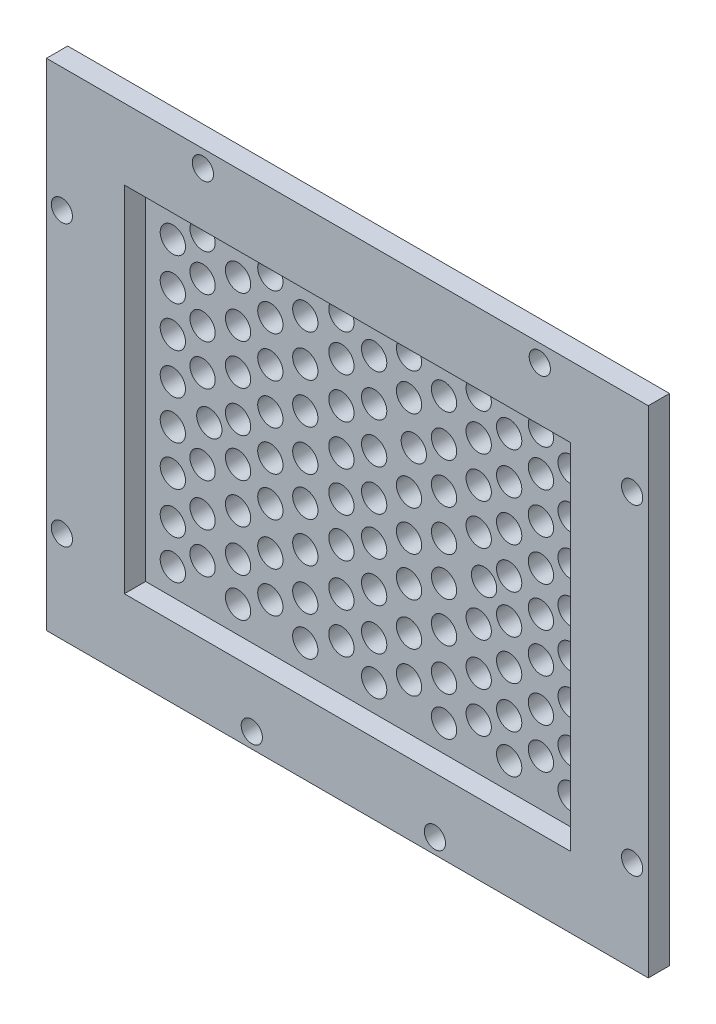
SolidWorks part; units mm, degrees
ref_plane "Front Plane" through (0, 0, 0) normal (0, 0, 1) x (1, 0, 0)
ref_plane "Top Plane" through (0, 0, 0) normal (0, 1, 0) x (1, 0, 0)
ref_plane "Right Plane" through (0, 0, 0) normal (1, 0, 0) x (0, 0, -1)
sketch "Sketch1" plane through (0, 0, 0) normal (0, 0, 1) x (1, 0, 0)
  line L1 (-42.5, 35) -> (42.5, 35)
  line L2 (-42.5, 35) -> (-42.5, -35)
  line L3 (-42.5, -35) -> (42.5, -35)
  line L4 (42.5, 35) -> (42.5, -35)
  line L5 (-42.5, 35) -> (42.5, -35) construction
  line L6 (-42.5, -35) -> (42.5, 35) construction
  point P0 (0, 0)
  dimension "D1" = 85
  dimension "D2" = 70
extrude "Boss-Extrude1" add sketch "Sketch1" along normal blind 6
sketch "Sketch2" plane through (0, 0, 0) normal (0, 0, -1) x (-1, 0, 0)
  line L1 (38, -30.5) -> (-38, -30.5)
  line L2 (38, -30.5) -> (38, 30.5)
  line L3 (38, 30.5) -> (-38, 30.5)
  line L4 (-38, -30.5) -> (-38, 30.5)
  line L5 (38, -30.5) -> (-38, 30.5) construction
  line L6 (38, 30.5) -> (-38, -30.5) construction
  line L7 (32.5, -26.0855) -> (-32.5, -26.0855)
  line L8 (32.5, -26.0855) -> (32.5, 26.0855)
  line L9 (32.5, 26.0855) -> (-32.5, 26.0855)
  line L10 (-32.5, -26.0855) -> (-32.5, 26.0855)
  line L11 (32.5, -26.0855) -> (-32.5, 26.0855) construction
  line L12 (32.5, 26.0855) -> (-32.5, -26.0855) construction
  point P0 (0, 0)
  point P6 (0, 0)
  dimension "D1" = 76
  dimension "D2" = 61
  dimension "D3" = 65
extrude "Cut-Extrude1" cut sketch "Sketch2" against normal blind 5
sketch "Sketch8" plane through (0, 0, 6) normal (0, 0, 1) x (1, 0, 0)
  line L1 (-31.5, 25) -> (31.5, 25)
  line L2 (-31.5, 25) -> (-31.5, -25)
  line L3 (-31.5, -25) -> (31.5, -25)
  line L4 (31.5, 25) -> (31.5, -25)
  line L5 (-31.5, 25) -> (31.5, -25) construction
  line L6 (-31.5, -25) -> (31.5, 25) construction
  point P0 (0, 0)
  dimension "D1" = 63
  dimension "D2" = 50
extrude "Cut-Extrude2" cut sketch "Sketch8" against normal blind 3
sketch "Sketch19" plane through (0, 0, 0) normal (0, 0, -1) x (-1, 0, 0)
  line L1 (42.5, 35) -> (-42.5, 35)
  line L2 (42.5, 35) -> (42.5, -35)
  line L3 (42.5, -35) -> (-42.5, -35)
  line L4 (-42.5, 35) -> (-42.5, -35)
  line L5 (38, 30.5) -> (-38, 30.5)
  line L6 (38, 30.5) -> (38, -30.5)
  line L7 (38, -30.5) -> (-38, -30.5)
  line L8 (-38, 30.5) -> (-38, -30.5)
extrude "Cut-Extrude3" cut sketch "Sketch19" against normal blind 3
hole_wizard "9/64 (0.14063) Diameter Hole3" positions "Sketch16" profile "Sketch17" hole size "9/64" standard "ANSI Inch" end condition through all
sketch "Sketch16" plane through (0, 0, 3) normal (0, 0, 1) x (1, 0, 0)
  point P0 (28.5299, -21.2502)
  point P2 (28.5299, -15.7459)
  point P4 (28.5299, -9.8359)
  point P6 (28.5299, -4.1565)
  point P8 (28.5299, 1.3478)
  point P10 (28.5299, 7.1342)
  point P12 (28.5299, 12.8672)
  point P14 (28.5299, 18.7586)
  point P16 (24.3337, 16.0835)
  point P18 (24.3337, 21.3242)
  point P20 (24.3337, 10.3073)
  point P22 (24.3337, 4.5476)
  point P24 (24.3337, -1.0885)
  point P26 (24.3337, -6.6814)
  point P28 (24.3337, -12.7046)
  point P30 (24.3337, -18.4375)
  point P32 (19.8485, -21.2502)
  point P34 (19.8485, -15.7459)
  point P36 (19.8485, -9.8359)
  point P38 (19.8485, -4.1565)
  point P40 (19.8485, 1.3478)
  point P42 (19.8485, 7.1342)
  point P44 (19.8485, 12.8672)
  point P46 (19.8485, 18.7586)
  point P48 (15.5475, 21.3242)
  point P50 (15.5475, 16.0835)
  point P52 (15.5475, 10.3073)
  point P54 (15.5475, 4.5476)
  point P56 (16.308, -1.0885)
  point P58 (15.5475, -6.6814)
  point P60 (15.5475, -12.7046)
  point P62 (15.5475, -18.4375)
  point P64 (10.6485, -21.2502)
  point P66 (10.6485, -15.7459)
  point P68 (10.6485, -9.8359)
  point P70 (10.6485, -4.1565)
  point P72 (10.6485, 1.3478)
  point P74 (10.6485, 7.1342)
  point P76 (10.6485, 12.8672)
  point P78 (10.6485, 18.7586)
  point P80 (5.7056, 21.3242)
  point P82 (5.7056, 16.0835)
  point P84 (6.3821, 10.3073)
  point P86 (5.7056, 4.5476)
  point P88 (5.7056, -1.0885)
  point P90 (5.7056, -6.6814)
  point P92 (5.7056, -12.7046)
  point P94 (5.7056, -18.4375)
  point P96 (0.7819, -21.2502)
  point P98 (0.7819, -15.7459)
  point P100 (0.7819, -9.8359)
  point P102 (0.7819, -4.1565)
  point P104 (0.7819, 1.3478)
  point P106 (0.7819, 7.1342)
  point P108 (0.7819, 12.8672)
  point P110 (0.7819, 18.7586)
  point P112 (-3.8442, 21.3242)
  point P114 (-3.8442, 16.0835)
  point P116 (-3.8442, 10.3073)
  point P118 (-3.8442, 4.5476)
  point P120 (-3.8442, -1.0885)
  point P122 (-3.8442, -6.6814)
  point P124 (-3.8442, -12.7046)
  point P126 (-3.8442, -18.4375)
  point P128 (-8.9449, -21.2502)
  point P130 (-8.9449, -15.7459)
  point P132 (-8.9449, -9.8359)
  point P134 (-8.9449, -4.1565)
  point P136 (-8.9449, 1.3478)
  point P138 (-8.9449, 7.1342)
  point P140 (-8.9449, 12.8672)
  point P142 (-8.9449, 18.7586)
  point P144 (-13.8796, 21.3242)
  point P146 (-13.8796, 16.0835)
  point P148 (-13.8796, 10.3073)
  point P150 (-13.8796, 4.5476)
  point P152 (-13.8796, -1.0885)
  point P154 (-13.8796, -6.6814)
  point P156 (-13.8796, -12.7046)
  point P158 (-13.8796, -18.4375)
  point P160 (-18.4432, -21.2502)
  point P162 (-18.4432, -15.7459)
  point P164 (-18.4432, -9.8359)
  point P166 (-18.4432, -4.1565)
  point P168 (-18.4432, 1.3478)
  point P170 (-18.4432, 7.1342)
  point P172 (-18.4432, 12.8672)
  point P174 (-18.4432, 18.7586)
  point P176 (-23.4561, 21.3242)
  point P178 (-23.4561, 16.0835)
  point P180 (-23.4561, 10.3073)
  point P182 (-23.4561, 4.5476)
  point P184 (-22.5022, -1.0885)
  point P186 (-23.4561, -6.6814)
  point P188 (-23.4561, -12.7046)
  point P190 (-23.4561, -18.4375)
  point P192 (-27.6514, -21.2502)
  point P194 (-27.6514, -15.7459)
  point P196 (-27.6514, -9.8359)
  point P198 (-27.6514, -4.1565)
  point P200 (-27.6514, 1.3478)
  point P202 (-27.6514, 7.1342)
  point P204 (-27.6514, 12.8672)
  point P206 (-27.6514, 18.7586)
sketch "Sketch17" plane through (28.5299, -21.2502, 3) normal (1, 0, 0) x (0, -1, 0)
  line L0 (0, 0) -> (0, 3)
  line L1 (0, 3) -> (1.786, 3)
  line L2 (1.786, 3) -> (1.786, 0)
  line L5 (1.786, 0) -> (0, 0)
  line L11 (0, -6.35) -> (0, 107.95) construction
  dimension "Thru Hole Dia." = 3.572
  dimension "Thru Hole Depth" = 3
hole_wizard "Ø3.0mm Dowel Hole1" positions "Sketch24" profile "Sketch25" hole size "Ø3.0" standard "ANSI Metric" end condition up to next
sketch "Sketch24" plane through (0, 0, 3) normal (0, 0, -1) x (-1, 0, 0)
  point P0 (13.4989, -32.8457)
  point P2 (-12.3633, -32.8457)
  point P4 (40.3256, -22.041)
  point P6 (40.3256, 17.4959)
  point P8 (20.4097, 32.5889)
  point P10 (-27.1767, 32.5889)
  point P12 (-40.218, 23.3314)
  point P14 (-40.218, -22.041)
sketch "Sketch25" plane through (-13.4989, -32.8457, 3) normal (1, 0, 0) x (0, 1, 0)
  line L0 (0, 0) -> (0, 3)
  line L1 (0, 3) -> (1.5, 3)
  line L2 (1.5, 3) -> (1.5, 0)
  line L5 (1.5, 0) -> (0, 0)
  line L11 (0, -6.35) -> (0, 107.95) construction
  dimension "Thru Hole Dia." = 3
  dimension "Thru Hole Depth" = 3
